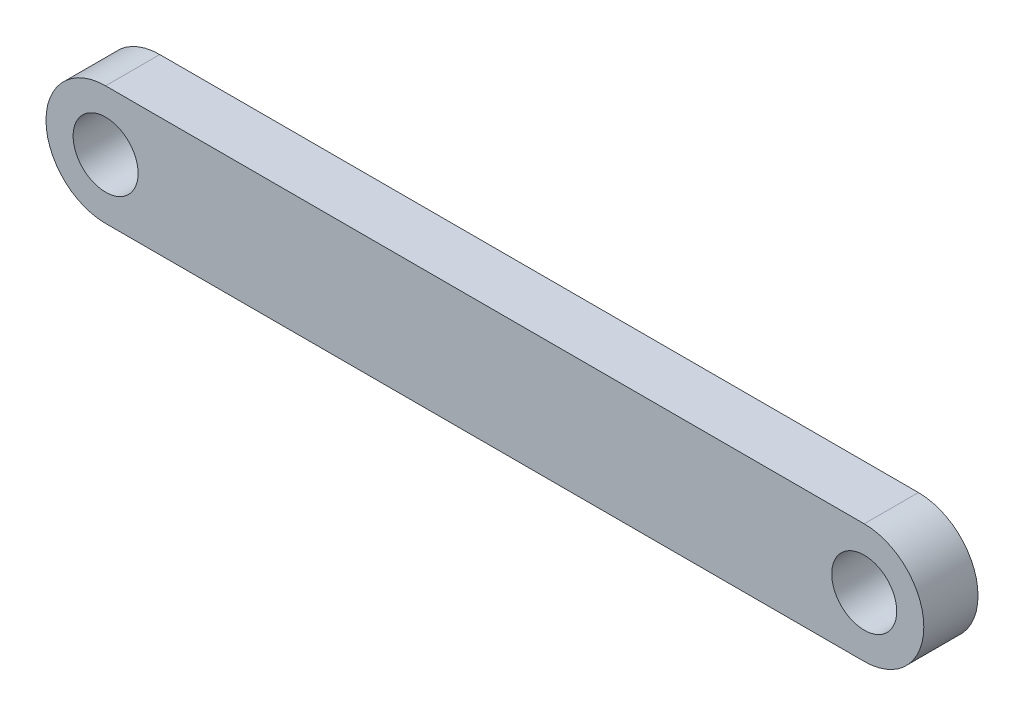
SolidWorks part; units mm, degrees
ref_plane "Front Plane" through (0, 0, 0) normal (0, 0, 1) x (1, 0, 0)
ref_plane "Top Plane" through (0, 0, 0) normal (0, 1, 0) x (1, 0, 0)
ref_plane "Right Plane" through (0, 0, 0) normal (1, 0, 0) x (0, 0, -1)
sketch "Sketch1" plane through (0, 0, 0) normal (0, 0, 1) x (1, 0, 0)
  line L0 (35, 0) -> (-35, 0) construction
  line L1 (35, -5.5) -> (-35, -5.5)
  line L2 (35, 5.5) -> (-35, 5.5)
  arc A0 (35, -5.5) -> (35, 5.5) centre (35, 0) ccw
  arc A1 (-35, 5.5) -> (-35, -5.5) centre (-35, 0) ccw
  circle A2 centre (35, 0) radius 3
  circle A3 centre (-35, 0) radius 3
  point P3 (0, 0)
  dimension "D3" = 6
  dimension "D1" = 11
  dimension "D2" = 70
extrude "Boss-Extrude1" add sketch "Sketch1" along normal mid plane 5
